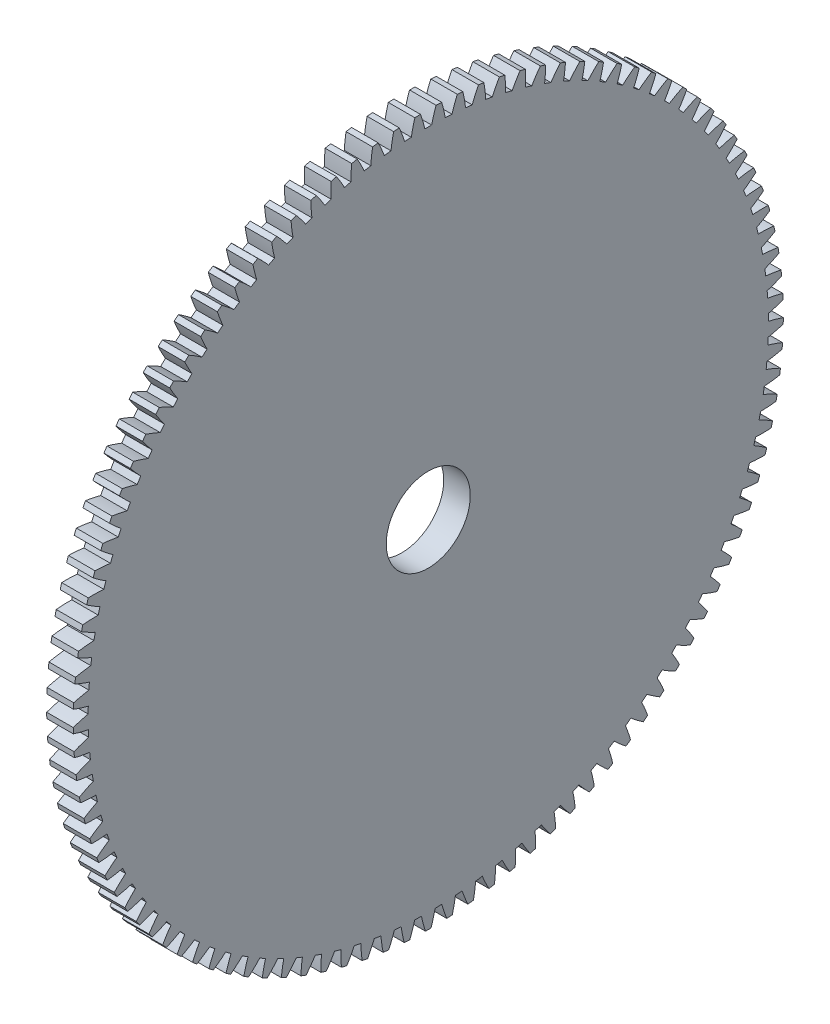
SolidWorks part; units mm, degrees
ref_plane "Plane1" through (0, 0, 0) normal (0, 0, 1) x (1, 0, 0)
ref_plane "Plane2" through (0, 0, 0) normal (0, 1, 0) x (1, 0, 0)
ref_plane "Plane3" through (0, 0, 0) normal (1, 0, 0) x (0, 0, -1)
sketch "HoldingSke" plane through (0, 0, 0) normal (0, 1, 0) x (1, 0, 0)
  line L0 (0, 0) -> (-0.0863, -0.322)
  line L1 (-15, 0) -> (100, 0) construction
  line L2 (0, 0) -> (-2.1039, 2.3779)
  line L3 (0, 0) -> (-11.863, 4.5341)
  line L4 (0, 0) -> (-2.2352, 8.3417)
  line L5 (0, 0) -> (-46.8476, -17.4728)
  line L6 (0, 0) -> (-9.9476, -6.7116)
  line L7 (-2.1039, 2.3779) -> (8.6586, 51.2059)
  line L8 (-76.2, 54.61) -> (-72.9, 54.61)
  line L9 (-67.7845, 28.3722) -> (-49.3413, 33.142)
  line L10 (-76.2, 71.12) -> (104.1128, 71.12)
  line L11 (0, 0) -> (-12, 0)
  line L12 (-76.2, 101.6) -> (-76.093, 101.6)
  line L13 (24.9733, 27.94) -> (52.9518, 28.4284)
  line L14 (24.9733, 27.94) -> (24.9743, 27.94)
  line L15 (24.9733, 27.94) -> (100.4006, 29.5858)
  line L16 (-63.627, -3) -> (-12.827, -3)
  circle A0 centre (0, 0) radius 19
  circle A1 centre (0, 0) radius 37.5
  circle A2 centre (0, 0) radius 37.5
  circle A3 centre (0, 0) radius 19
  dimension "MHD" = 75
  dimension "Hub_dia" = 75
  dimension "Bore" = 38
  dimension "MBD" = 38
  dimension "Num_teeth" = 105
  dimension "Pitch" = 0.3333
  dimension "Overall_len" = 50
  dimension "Show_teeth" = 105
  dimension "Thickness" = 12
  dimension "OAL" = 50.0001
  dimension "T_dim" = 3.3
  dimension "Ap" = 14.5
  dimension "H" = 19.05
  dimension "Pitch_radius" = 180.3128
  dimension "Width" = 12
  dimension "Backlash" = 0.107
  dimension "Addendum_fac" = 1
  dimension "Dedendum_fac" = 1.25
  dimension "Clearance_fac" = 0.25
  dimension "Dedendum_add" = 0.001
  dimension "Module" = 3
sketch "BasProSke" plane through (0, 0, 0) normal (0, 1, 0) x (1, 0, 0)
  line L0 (-10, 0) -> (60, 0) construction
  line L1 (0, 0) -> (0, 160.5)
  line L2 (0, 0) -> (12, 0)
  line L3 (12, 0) -> (12, 160.5)
  line L4 (12, 160.5) -> (0, 160.5)
  dimension "Thickness" = 12
  dimension "Diameter" = 321
revolve "Base-Revolve" add sketch "BasProSke" angle 360 about L0
sketch "TooCutSke" plane through (0, 0, 0) normal (1, 0, 0) x (0, 0, -1)
  line L1 (0, 0) -> (0, 107) construction
  line L2 (0, 0) -> (-2.5434, 157.4795) construction
  line L3 (0, 0) -> (-9.4225, 314.8292) construction
  line L4 (-2.5434, 157.4795) -> (-4.7112, 157.4146) construction
  arc A0 (1.519, 153.7415) -> (-1.519, 153.7415) centre (0, 0) ccw
  arc A1 (3.5511, 160.4861) -> (-3.5511, 160.4861) centre (0, 0) ccw
  circle A2 centre (0, 0) radius 157.5 construction
  circle A3 centre (0, 0) radius 152.4833 construction
  arc A4 (-1.519, 153.7415) -> (-3.5511, 160.4861) centre (-62.7623, 138.9678) ccw
  arc A5 (3.5511, 160.4861) -> (1.519, 153.7415) centre (62.7623, 138.9678) ccw
  dimension "Root_dia" = 307.498
  dimension "Overcut_dia" = 321.0508
  dimension "Pitch_dia" = 315
  dimension "Base_dia" = 304.9665
  dimension "Flank_rad" = 63
  dimension "Half_ang" = 1.714
  dimension "Half_CT" = 2.1689
extrude "ToothCut" cut sketch "TooCutSke" along normal through all
fillet "Breaks" [suppressed] radius 0.06
fillet "RootFillets" [suppressed] radius 0.751
pattern_circular "TeethCuts" count 105 every 3.429 about axis through (-10, 0, 0) along (1, 0, 0) of "ToothCut", "RootFillets", "Breaks"
sketch "HubNeaOneSke" plane through (0, 0, 0) normal (-1, 0, 0) x (0, 0, 1)
  circle A0 centre (0, 0) radius 37.5
  dimension "Diameter" = 75
extrude "HubNearOne" [suppressed] add sketch "HubNeaOneSke" along normal blind 38.0001
sketch "HubNeaBotSke" plane through (0, 0, 0) normal (-1, 0, 0) x (0, 0, 1)
  circle A0 centre (0, 0) radius 37.5
  dimension "Diameter" = 75
extrude "HubNearBoth" [suppressed] add sketch "HubNeaBotSke" along normal blind 19
ref_plane "FarPln" through (12, 0, 0) normal (1, 0, 0) x (0, 0, -1)
sketch "HubFarSke" plane through (12, 0, 0) normal (1, 0, 0) x (0, 0, -1)
  circle A0 centre (0, 0) radius 37.5
  dimension "Diameter" = 75
extrude "HubFar" [suppressed] add sketch "HubFarSke" along normal blind 19
sketch "BorSke" plane through (0, 0, 0) normal (1, 0, 0) x (0, 0, -1)
  circle A0 centre (0, 0) radius 19
  dimension "Diameter" = 38
extrude "Bore" cut sketch "BorSke" along normal mid plane 100.0001
sketch "KeySke" plane through (0, 0, 0) normal (1, 0, 0) x (0, 0, -1)
  line L0 (-6, 0) -> (-6, 22.3)
  line L1 (-6, 22.3) -> (6, 22.3)
  line L2 (6, 22.3) -> (6, 0)
  line L3 (0, 0) -> (0, 34) construction
  line L4 (-6, 0) -> (6, 0)
  dimension "Width" = 12
  dimension "Offset" = 22.3
extrude "Keyway" [suppressed] cut sketch "KeySke" along normal mid plane 100.0001
pattern_circular "Keyway2" [suppressed] count 2 every 90 about axis through (-10, 0, 0) along (1, 0, 0)
equation "' \"Module@HoldingSke\" = 6.35"
equation "' \"Num_teeth@HoldingSke\" = 12"
equation "' \"Ap@HoldingSke\" =  20"
equation "' \"Ap@HoldingSke\" = 20"
equation "' \"Width@HoldingSke\" = 0.5 * 25.4"
equation "' \"Hub_dia@HoldingSke\"= 1 * 25.4"
equation "' \"Hub_dia@HoldingSke\" = 1 * 25.4"
equation "' \"Overall_len@HoldingSke\" = 1.0 * 25.4"
equation "' \"Bore@HoldingSke\" = 0.75 * 25.4"
equation "' \"T_dim@HoldingSke\" = 0.1 * 25.4"
equation "' \"Width@KeySke\" = 0.25 * 25.4"
equation "' \"Show_teeth@HoldingSke\" = 13"
equation "' \"Backlash@HoldingSke\" = 0.009 * 25.4"
equation "' \"Addendum_fac@HoldingSke\" = 1.0"
equation "' \"Dedendum_fac@HoldingSke\" = 1.25"
equation "' \"Dedendum_add@HoldingSke\" = 0.00005 * 25.4"
equation "' \"Clearance_fac@HoldingSke\" = 0.25"
equation "\"Pitch@HoldingSke\" = 1 / \"Module@HoldingSke\""
equation "\"Overcut_dia@TooCutSke\" = (\"Num_teeth@HoldingSke\" + 2 * \"Addendum_fac@HoldingSke\") / \"Pitch@HoldingSke\" + 0.002 * 25.4"
equation "\"Pitch_dia@TooCutSke\" = \"Num_teeth@HoldingSke\" / \"Pitch@HoldingSke\""
equation "\"Base_dia@TooCutSke\" = \"Num_teeth@HoldingSke\" / \"Pitch@HoldingSke\" * cos((\"Ap@HoldingSke\"  * 3.14159265 / 180))"
equation "\"Root_dia@TooCutSke\" = (\"Num_teeth@HoldingSke\" + 2) / \"Pitch@HoldingSke\" - 2 * (\"Addendum_fac@HoldingSke\" + \"Dedendum_fac@HoldingSke\") / \"Pitch@HoldingSke\" - \"Dedendum_add@HoldingSke\" * 2"
equation "\"Half_ang@TooCutSke\" = 180 / \"Num_teeth@HoldingSke\""
equation "\"Half_CT@TooCutSke\" = \"Num_teeth@HoldingSke\" / \"Pitch@HoldingSke\" * sin((3.14159265 / 2 / \"Num_teeth@HoldingSke\")) / 2 - 7 * \"Backlash@HoldingSke\" / 4"
equation "\"Flank_rad@TooCutSke\" = \"Num_teeth@HoldingSke\" / \"Pitch@HoldingSke\" / 5"
equation "\"Radius@RootFillets\" = \"Clearance_fac@HoldingSke\" / \"Pitch@HoldingSke\" + \"Dedendum_add@HoldingSke\""
equation "\"Break_rad@Breaks\" = 0.02 / \"Pitch@HoldingSke\""
equation "\"Thickness@HoldingSke\" = \"Width@HoldingSke\""
equation "\"OAL@HoldingSke\" = \"Thickness@HoldingSke\""
equation "\"MHD@HoldingSke\" = (\"Num_teeth@HoldingSke\" + 2) / \"Pitch@HoldingSke\" - 2 * (\"Addendum_fac@HoldingSke\" + \"Dedendum_fac@HoldingSke\")  / \"Pitch@HoldingSke\" - \"Dedendum_add@HoldingSke\" * 2"
equation "\"MBD@HoldingSke\" = (\"Num_teeth@HoldingSke\" + 2) / \"Pitch@HoldingSke\" - 2 * (\"Addendum_fac@HoldingSke\" + \"Dedendum_fac@HoldingSke\")  / \"Pitch@HoldingSke\" - \"Dedendum_add@HoldingSke\" * 2 - 0.002 * 25.4"
equation "\"MHD@HoldingSke\" = ((sgn( \"MHD@HoldingSke\" - \"Hub_dia@HoldingSke\" )-1)*( \"MHD@HoldingSke\" - \"Hub_dia@HoldingSke\" ))/-2+ \"Hub_dia@HoldingSke\""
equation "\"MBD@HoldingSke\" = ((sgn( \"MBD@HoldingSke\" - \"Bore@HoldingSke\" )-1)*( \"MBD@HoldingSke\" - \"Bore@HoldingSke\" ))/-2+ \"Bore@HoldingSke\""
equation "\"OAL@HoldingSke\" = ((sgn( \"OAL@HoldingSke\" - \"Overall_len@HoldingSke\" )+1)*( \"OAL@HoldingSke\" - \"Overall_len@HoldingSke\" ))/2 + \"Overall_len@HoldingSke\" + 0.000002 * 25.4"
equation "\"Num_teeth@TeethCuts\" = int( \"Show_teeth@HoldingSke\" ) + 1"
equation "\"Num_teeth@TeethCuts\" = ((sgn( \"Num_teeth@TeethCuts\" - \"Num_teeth@HoldingSke\" )-1)*( \"Num_teeth@TeethCuts\" - \"Num_teeth@HoldingSke\" ))/-2+ \"Num_teeth@HoldingSke\""
equation "\"Num_teeth@TeethCuts\" = ((sgn( \"Num_teeth@TeethCuts\" - 2.0)+1)*( \"Num_teeth@TeethCuts\" - 2.0))/2 +2.0"
equation "\"Angle@TeethCuts\" = 360.0 / \"Num_teeth@HoldingSke\""
equation "\"Diameter@BasProSke\" = (\"Num_teeth@HoldingSke\" + 2 * \"Addendum_fac@HoldingSke\") / \"Pitch@HoldingSke\""
equation "\"Thickness@BasProSke\"  = \"Thickness@HoldingSke\""
equation "' \"Fillet_rad@BasProSke\" =  \"Thickness@HoldingSke\" * 0.05"
equation "' \"Fillet_rad@BasProSke\" = \"Thickness@HoldingSke\" * 0.05"
equation "\"MHD@HoldingSke\" = ((sgn( \"MHD@HoldingSke\" - \"Root_dia@TooCutSke\" )-1)*( \"MHD@HoldingSke\" - \"Root_dia@TooCutSke\" ))/-2+ \"Root_dia@TooCutSke\""
equation "\"Diameter@HubNeaOneSke\" = \"MHD@HoldingSke\""
equation "\"Length@HubNearOne\" = \"OAL@HoldingSke\" - \"Thickness@BasProSke\""
equation "\"Diameter@HubNeaBotSke\" = \"MHD@HoldingSke\""
equation "\"Length@HubNearBoth\" = ( \"OAL@HoldingSke\" - \"Thickness@BasProSke\" ) / 2.0"
equation "\"Thickness@FarPln\" = \"Thickness@BasProSke\""
equation "\"Diameter@HubFarSke\" = \"MHD@HoldingSke\""
equation "\"Length@HubFar\" = ( \"OAL@HoldingSke\" - \"Thickness@BasProSke\" ) / 2.0"
equation "\"Diameter@BorSke\" = \"MBD@HoldingSke\""
equation "\"D1@Bore\" = \"OAL@HoldingSke\" * 2.0"
equation "\"D1@Keyway\" = \"OAL@HoldingSke\" * 2.0"
equation "\"Offset@KeySke\" = \"T_dim@HoldingSke\" + \"MBD@HoldingSke\" / 2.0"
